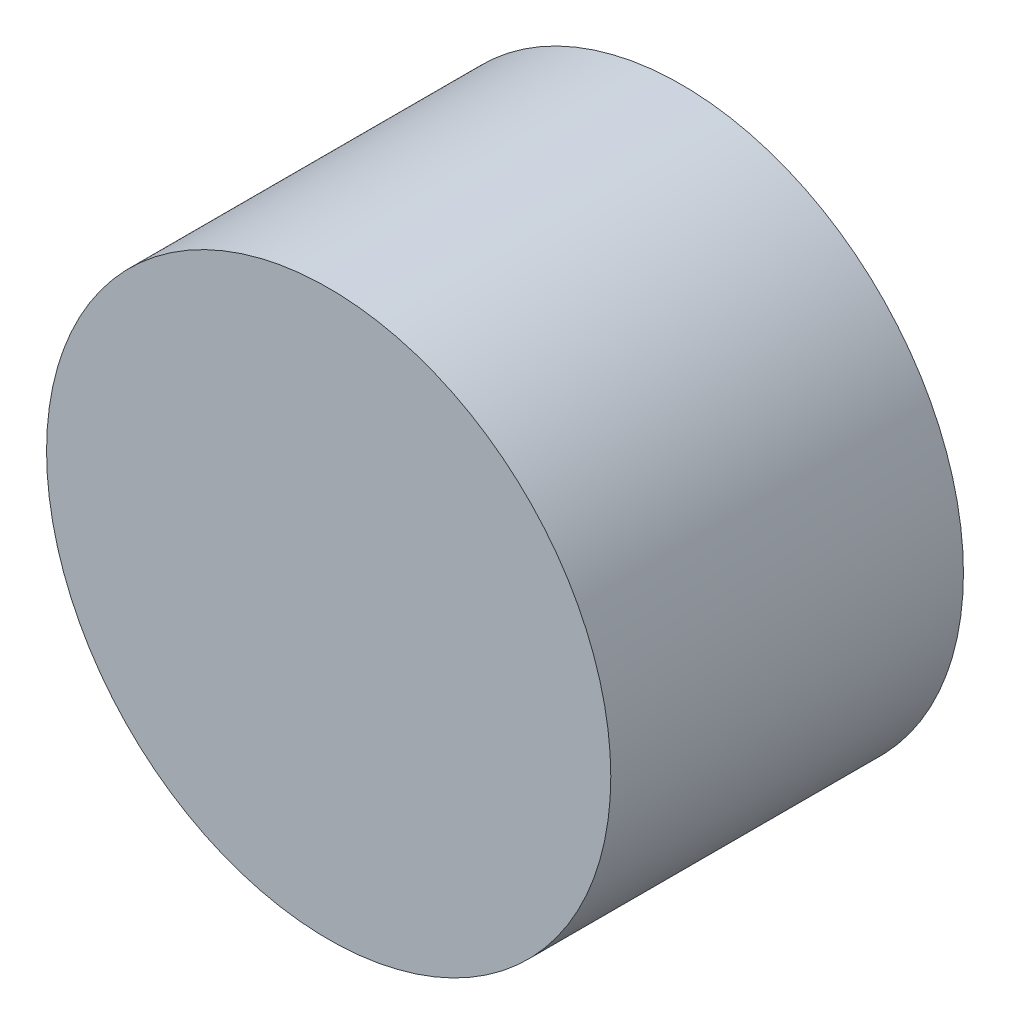
SolidWorks part; units mm, degrees
ref_plane "Front Plane" through (0, 0, 0) normal (0, 0, 1) x (1, 0, 0)
ref_plane "Top Plane" through (0, 0, 0) normal (0, 1, 0) x (1, 0, 0)
ref_plane "Right Plane" through (0, 0, 0) normal (1, 0, 0) x (0, 0, -1)
sketch "Sketch1" plane through (0, 0, 0) normal (0, 0, 1) x (1, 0, 0)
  circle A0 centre (0, 0) radius 40.64
  dimension "D1" = 81.28
extrude "Boss-Extrude1" add sketch "Sketch1" along normal blind 50.8
